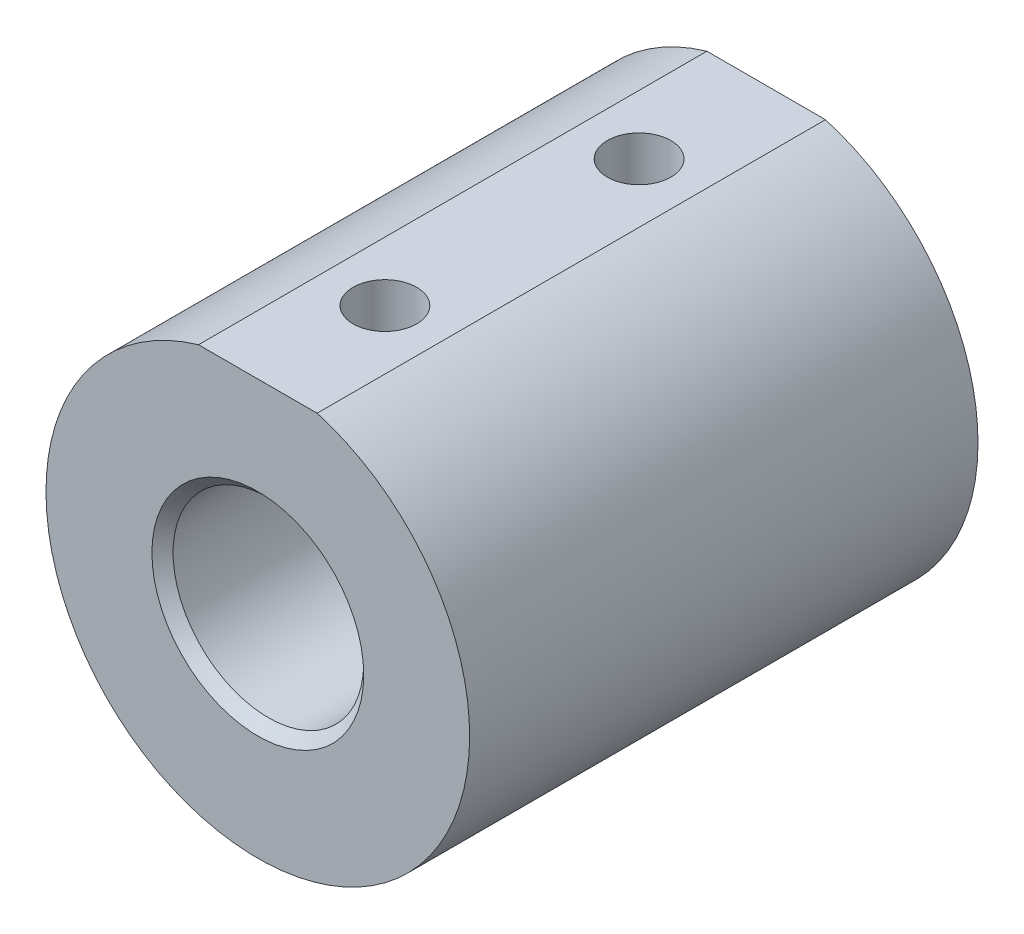
SolidWorks part; units mm, degrees
material "PE High Density"
ref_plane "Front Plane" through (0, 0, 0) normal (0, 0, 1) x (1, 0, 0)
ref_plane "Top Plane" through (0, 0, 0) normal (0, 1, 0) x (1, 0, 0)
ref_plane "Right Plane" through (0, 0, 0) normal (1, 0, 0) x (0, 0, -1)
sketch "Sketch1" plane through (0, 0, 0) normal (0, 0, 1) x (1, 0, 0)
  line L0 (0, 12.7) -> (0, 30.48) construction
  line L1 (-8.89, 30.48) -> (8.89, 30.48)
  circle A0 centre (0, 0) radius 14.2875
  circle A1 centre (0, 0) radius 31.75
  circle A2 centre (0, 0) radius 12.7 construction
  point P15 (0, 30.48)
  dimension "D1" = 28.575
  dimension "D2" = 25.4
  dimension "D3" = 62.23
  dimension "D5" = 63.5
  dimension "D4" = 17.78
extrude "Boss-Extrude1" add sketch "Sketch1" along normal blind 76.2 contours L1 A1 A0
sketch "Sketch2" plane through (0, 30.48, 0) normal (0, 1, 0) x (1, 0, 0)
  line L0 (-8.89, -76.2) -> (-8.89, 0) construction
  line L3 (-8.89, -38.1) -> (8.89, -38.1) construction
  line L4 (8.89, -76.2) -> (8.89, 0) construction
  line L5 (0, -57.15) -> (0, -19.05) construction
  circle A0 centre (0, -57.15) radius 4.7625
  circle A1 centre (0, -19.05) radius 4.7625
  point P0 (0, -38.1)
  point P12 (0, -38.1)
  dimension "D1" = 9.525
  dimension "D2" = 9.525
  dimension "D3" = 38.1
extrude "Cut-Extrude1" cut sketch "Sketch2" against normal up to next
chamfer "Chamfer1" distance 1.5875 angle 45 2 edges at (14.2875, 0, 0) (14.2875, 0, 76.2)
